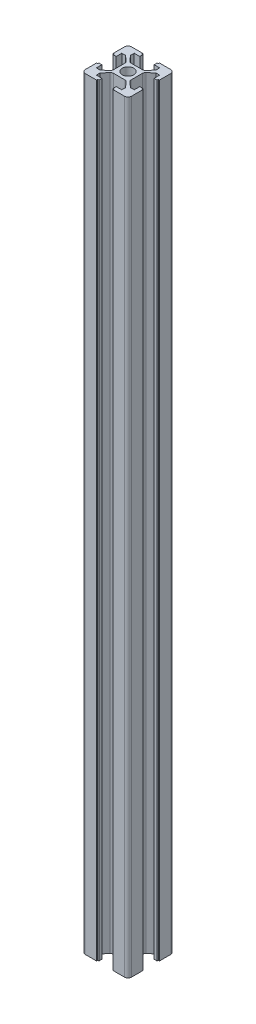
SolidWorks part; units mm, degrees
ref_plane "Front Plane" through (0, 0, 0) normal (0, 0, 1) x (1, 0, 0)
ref_plane "Top Plane" through (0, 0, 0) normal (0, 1, 0) x (1, 0, 0)
ref_plane "Right Plane" through (0, 0, 0) normal (1, 0, 0) x (0, 0, -1)
sketch "Sketch1" plane through (0, 0, 0) normal (0, 1, 0) x (1, 0, 0)
  line L0 (10, 0) -> (3.8, 0) construction
  line L1 (-8.5, -10) -> (8.5, -10)
  line L2 (-10, -8.5) -> (-10, 8.5)
  line L3 (-8.5, 10) -> (8.5, 10)
  line L4 (10, -8.5) -> (10, -3.6)
  line L5 (-10, -10) -> (10, 10) construction
  line L6 (-10, 10) -> (10, -10) construction
  line L7 (3.8, -2.4101) -> (3.8, 2.4101)
  line L8 (9.5, -3.1) -> (9.5, 3.1)
  line L9 (9.5, 3.1) -> (8.2, 3.1)
  line L10 (9.5, 3.1) -> (9.5, 3.6)
  line L11 (9.5, -3.1) -> (9.5, -3.6)
  line L12 (9.5, -3.6) -> (10, -3.6)
  line L13 (9.5, 3.6) -> (10, 3.6)
  line L14 (10, 3.6) -> (10, 8.5)
  line L15 (9.5, -3.1) -> (8.2, -3.1)
  line L16 (8.2, -3.1) -> (3.8, -3.1) construction
  line L17 (8.2, 3.1) -> (3.8, 3.1) construction
  line L18 (8.2, 3.1) -> (8.2, 5.5)
  line L19 (8.2, -3.1) -> (8.2, -5.5)
  line L20 (8.2, -5.5) -> (6.6, -5.5)
  line L21 (8.2, 5.5) -> (6.6, 5.5)
  line L22 (6.6, 5.5) -> (4.3238, 3.549)
  line L23 (6.6, -5.5) -> (4.3238, -3.549)
  line L24 (-5.5, -6.6) -> (-3.549, -4.3238)
  line L25 (-5.5, -8.2) -> (-5.5, -6.6)
  line L26 (-3.1, -8.2) -> (-5.5, -8.2)
  line L27 (-2.4101, -3.8) -> (2.4101, -3.8)
  line L28 (5.5, -6.6) -> (3.549, -4.3238)
  line L29 (5.5, -8.2) -> (5.5, -6.6)
  line L30 (3.1, -8.2) -> (5.5, -8.2)
  line L31 (3.1, -9.5) -> (3.1, -8.2)
  line L32 (3.1, -9.5) -> (3.6, -9.5)
  line L33 (3.6, -9.5) -> (3.6, -10)
  line L34 (-3.6, -9.5) -> (-3.6, -10)
  line L35 (-3.1, -9.5) -> (-3.6, -9.5)
  line L36 (-3.1, -9.5) -> (-3.1, -8.2)
  line L37 (-6.6, 5.5) -> (-4.3238, 3.549)
  line L38 (-8.2, 5.5) -> (-6.6, 5.5)
  line L39 (-8.2, 3.1) -> (-8.2, 5.5)
  line L40 (-3.8, 2.4101) -> (-3.8, -2.4101)
  line L41 (-6.6, -5.5) -> (-4.3238, -3.549)
  line L42 (-8.2, -5.5) -> (-6.6, -5.5)
  line L43 (-8.2, -3.1) -> (-8.2, -5.5)
  line L44 (-9.5, -3.1) -> (-8.2, -3.1)
  line L45 (-9.5, -3.1) -> (-9.5, -3.6)
  line L46 (-9.5, -3.6) -> (-10, -3.6)
  line L47 (-9.5, 3.6) -> (-10, 3.6)
  line L48 (-9.5, 3.1) -> (-9.5, 3.6)
  line L49 (-9.5, 3.1) -> (-8.2, 3.1)
  line L50 (5.5, 6.6) -> (3.549, 4.3238)
  line L51 (5.5, 8.2) -> (5.5, 6.6)
  line L52 (3.1, 8.2) -> (5.5, 8.2)
  line L53 (2.4101, 3.8) -> (-2.4101, 3.8)
  line L54 (-5.5, 6.6) -> (-3.549, 4.3238)
  line L55 (-5.5, 8.2) -> (-5.5, 6.6)
  line L56 (-3.1, 8.2) -> (-5.5, 8.2)
  line L57 (-3.1, 9.5) -> (-3.1, 8.2)
  line L58 (-3.1, 9.5) -> (-3.6, 9.5)
  line L59 (-3.6, 9.5) -> (-3.6, 10)
  line L60 (3.6, 9.5) -> (3.6, 10)
  line L61 (3.1, 9.5) -> (3.6, 9.5)
  line L62 (3.1, 9.5) -> (3.1, 8.2)
  circle A0 centre (0, 0) radius 2.5
  arc A1 (8.5, 10) -> (10, 8.5) centre (8.5, 8.5) cw
  arc A2 (8.5, -10) -> (10, -8.5) centre (8.5, -8.5) ccw
  arc A3 (-8.5, -10) -> (-10, -8.5) centre (-8.5, -8.5) cw
  arc A4 (-10, 8.5) -> (-8.5, 10) centre (-8.5, 8.5) cw
  arc A5 (3.8, -2.4101) -> (4.3238, -3.549) centre (5.3, -2.4101) ccw
  arc A6 (4.3238, 3.549) -> (3.8, 2.4101) centre (5.3, 2.4101) ccw
  arc A7 (-2.4101, -3.8) -> (-3.549, -4.3238) centre (-2.4101, -5.3) ccw
  arc A8 (3.549, -4.3238) -> (2.4101, -3.8) centre (2.4101, -5.3) ccw
  arc A9 (-3.8, 2.4101) -> (-4.3238, 3.549) centre (-5.3, 2.4101) ccw
  arc A10 (-4.3238, -3.549) -> (-3.8, -2.4101) centre (-5.3, -2.4101) ccw
  arc A11 (2.4101, 3.8) -> (3.549, 4.3238) centre (2.4101, 5.3) ccw
  arc A12 (-3.549, 4.3238) -> (-2.4101, 3.8) centre (-2.4101, 5.3) ccw
  point P0 (0, 0)
  point P25 (3.8, 0)
  point P28 (8.5, 0)
  dimension "D3" = 5
  dimension "D4" = 1.5
  dimension "D5" = 1.5
  dimension "D1" = 20
  dimension "D2" = 20
  dimension "D6" = 6.2
  dimension "D7" = 6.2
  dimension "D8" = 0.5
  dimension "D9" = 1.3
  dimension "D10" = 4
extrude "Boss-Extrude1" add sketch "Sketch1" along normal blind 330 contours A12 L54 L55 L56 L57 L58 L59 L3 A4 L2 L47 L48 L49 L39 L38 L37 A9 L40 A10 L41 L42 L43 L44 L45 L46 A3 L1 L34 L35 L36 L26 L25 L24 A7 L27 A8 L28 L29 L30 L31 L32 L33 A2 L4 L12 L11 L15 L19 L20
